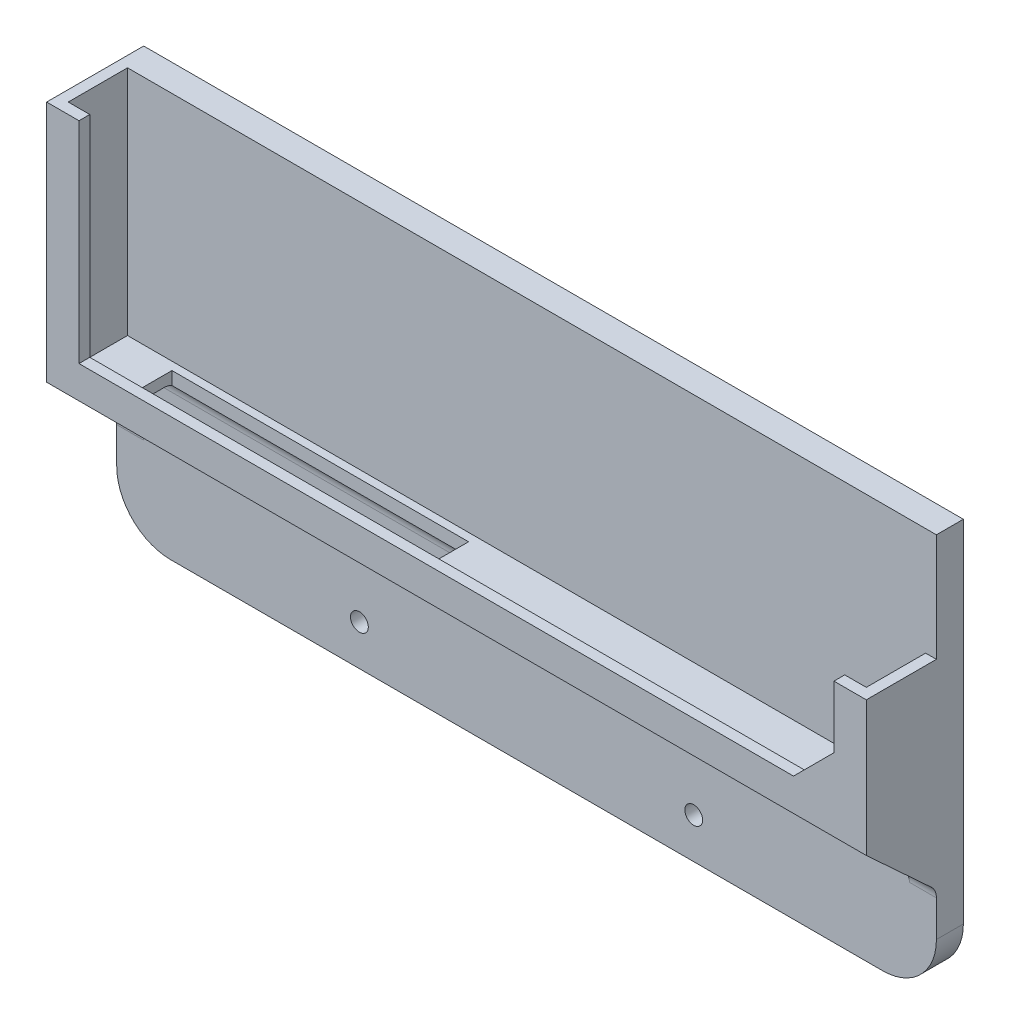
SolidWorks part; units mm, degrees
ref_plane "Front Plane" through (0, 0, 0) normal (0, 0, 1) x (1, 0, 0)
ref_plane "Top Plane" through (0, 0, 0) normal (0, 1, 0) x (1, 0, 0)
ref_plane "Right Plane" through (0, 0, 0) normal (1, 0, 0) x (0, 0, -1)
sketch "Sketch1" plane through (0, 0, 0) normal (0, 0, 1) x (1, 0, 0)
  line L1 (0, 0) -> (152, 0)
  line L2 (0, 0) -> (0, 15)
  line L3 (0, 15) -> (152, 15)
  line L4 (152, 0) -> (152, 15)
  line L5 (0, 15) -> (152, 15)
  line L6 (0, 15) -> (0, 75)
  line L7 (0, 75) -> (152, 75)
  line L8 (152, 15) -> (152, 75)
  circle A0 centre (45, 7.5) radius 1.65
  circle A1 centre (107, 7.5) radius 1.65
  dimension "D4" = 3.3
  dimension "D5" = 3.3
  dimension "D1" = 15
  dimension "D2" = 152
  dimension "D3" = 60
  dimension "D6" = 45
  dimension "D7" = 45
  dimension "D8" = 152
extrude "Boss-Extrude1" add sketch "Sketch1" along normal blind 5 contours L3 L8 L7 L6 | L1 L4 L3 L2
fillet "Fillet1" radius 10 2 edges at (152, 0, 2.5) (0, 0, 2.5)
sketch "Sketch2" plane through (0, 0, 5) normal (0, 0, 1) x (1, 0, 0)
  line L0 (152, 10) -> (152, 75) construction
  line L1 (0, 75) -> (2, 75)
  line L2 (0, 75) -> (0, 30)
  line L3 (0, 30) -> (152, 30)
  line L4 (152, 55) -> (152, 30)
  line L5 (2, 73) -> (2, 32)
  line L6 (2, 32) -> (150, 32)
  line L7 (150, 55) -> (150, 32)
  line L9 (2, 73) -> (2, 75)
  line L12 (0, 75) -> (152, 75) construction
  line L13 (2, 73) -> (150, 73) construction
  line L14 (150, 73) -> (150, 32) construction
  line L19 (152, 75) -> (152, 30) construction
  line L20 (0, 75) -> (152, 75) construction
  line L23 (152, 55) -> (150, 55)
  dimension "D1" = 45
  dimension "D2" = 2
  dimension "D3" = 20
extrude "Boss-Extrude2" add sketch "Sketch2" along normal blind 11
sketch "Sketch3" plane through (0, 0, 16) normal (0, 0, 1) x (1, 0, 0)
  line L0 (152, 30) -> (152, 55) construction
  line L1 (0, 75) -> (0, 30) construction
  line L2 (0, 30) -> (152, 30) construction
  line L3 (152, 30) -> (152, 55)
  line L4 (0, 75) -> (0, 30)
  line L5 (0, 30) -> (152, 30)
  line L6 (6, 75) -> (6, 36)
  line L7 (6, 36) -> (146, 36)
  line L8 (146, 36) -> (146, 55)
  line L9 (6, 75) -> (0, 75)
  line L10 (146, 55) -> (152, 55)
  dimension "D1" = 6
extrude "Boss-Extrude3" add sketch "Sketch3" along normal blind 2 contours L6 L7 L8 L10 L3 L5 L4 L9
chamfer "Chamfer1" distance 7.5 angle 45 1 edges at (146, 36, 17)
sketch "Sketch4" plane through (0, 0, 0) normal (-1, 0, 0) x (0, 0, 1)
  line L0 (18, 30) -> (5, 18)
  line L1 (5, 10) -> (5, 30) construction
  line L2 (18, 30) -> (5, 30)
  line L3 (5, 30) -> (5, 18)
extrude "Boss-Extrude4" add sketch "Sketch4" against normal blind 5 contours L0 L3 L2
ref_plane "Plane1" through (76, 0, 0) normal (-1, 0, 0) x (0, 0, 1)
mirror "Mirror1" about plane through (76, 0, 0) normal (-1, 0, 0) of "Boss-Extrude4"
fillet "Fillet2" radius 3 3 edges at (149.5, 18, 5) (76, 30, 5) (2.5, 18, 5)
sketch "Sketch5" plane through (0, 32, 0) normal (0, 1, 0) x (1, 0, 0)
  line L0 (76, -5) -> (76, -16)
  line L1 (150, -5) -> (2, -5) construction
  line L2 (150, -16) -> (2, -16) construction
  line L4 (11.7411, -14.5) -> (66.7411, -14.5)
  line L5 (11.7411, -14.5) -> (11.7411, -6.5)
  line L6 (11.7411, -6.5) -> (66.7411, -6.5)
  line L7 (66.7411, -14.5) -> (66.7411, -6.5)
  line L8 (11.7411, -14.5) -> (66.7411, -6.5) construction
  line L9 (11.7411, -6.5) -> (66.7411, -14.5) construction
  point P6 (39.2411, -10.5)
  dimension "D1" = 8
  dimension "D2" = 55
extrude "Cut-Extrude1" cut sketch "Sketch5" against normal blind 10 contours L4 L7 L6 L5
